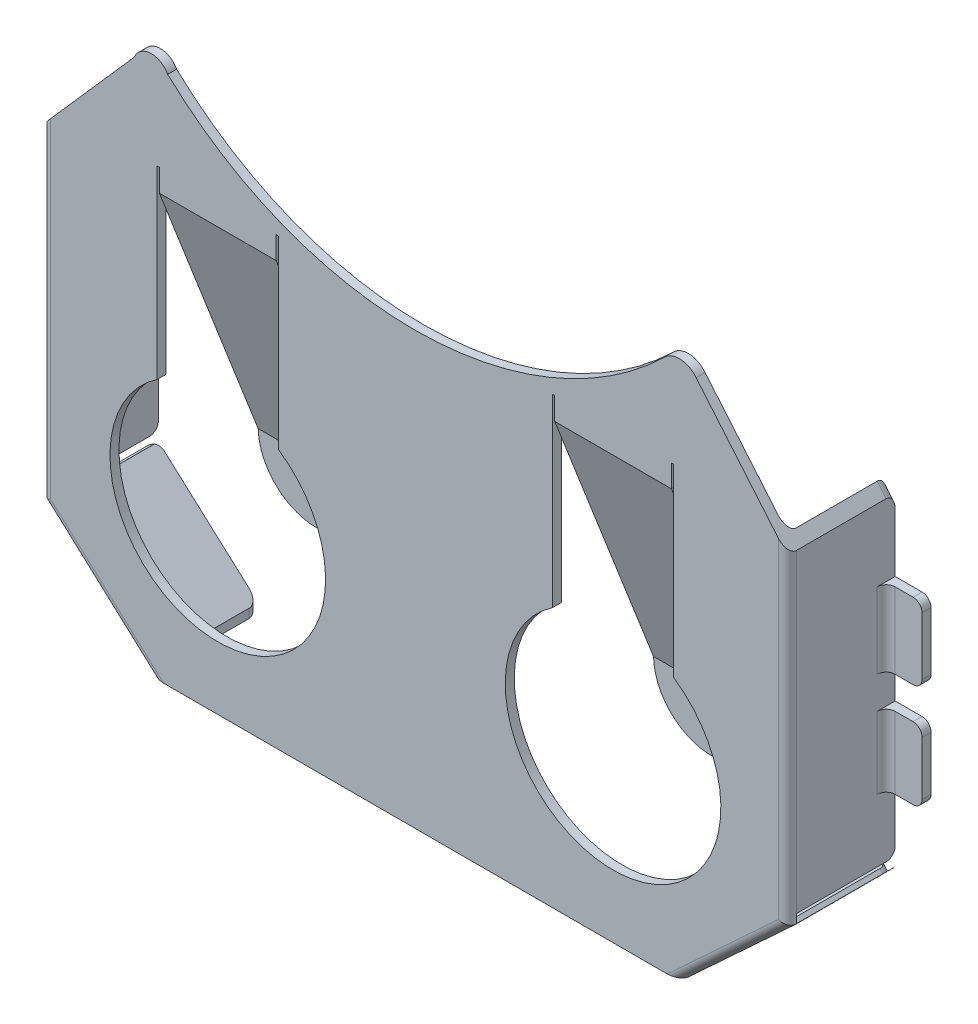
SolidWorks part; units mm, degrees
ref_plane "Front Plane" through (0, 0, 0) normal (0, 0, 1) x (1, 0, 0)
ref_plane "Top Plane" through (0, 0, 0) normal (0, 1, 0) x (1, 0, 0)
ref_plane "Right Plane" through (0, 0, 0) normal (1, 0, 0) x (0, 0, -1)
sketch "Sketch1" plane through (0, 0, 0) normal (0, 0, 1) x (1, 0, 0)
  line L0 (-0.8513, 0) -> (14.1347, 0)
  line L2 (-3.9254, 2.794) -> (-3.9254, 11.938)
  line L3 (-3.9254, 12.065) -> (17.1566, 12.065) construction
  line L4 (17.1566, 2.794) -> (17.1566, 11.938)
  line L5 (14.1347, 0) -> (14.1347, 15.2374)
  line L6 (-0.8513, 0) -> (-0.8513, 15.2392)
  line L7 (-3.9254, 11.938) -> (-1.3073, 14.913)
  line L8 (-0.8513, 0) -> (-3.9254, 2.794)
  line L9 (17.1566, 11.938) -> (14.5779, 15.0065)
  line L10 (14.1347, 0) -> (17.1566, 2.794)
  arc A2 (-0.3623, 14.9648) -> (13.6714, 15.0504) centre (6.6097, 22.3651) ccw
  arc A3 (-1.3073, 14.913) -> (-0.3623, 14.9648) centre (-0.8226, 14.7174) cw
  arc A5 (14.5779, 15.0065) -> (13.6714, 15.0504) centre (14.1059, 14.6414) ccw
  point P0 (-0.8513, 15.2392)
  dimension "D1" = 21.082
  dimension "D2" = 14.986
extrude "Boss-Extrude1" add sketch "Sketch1" along normal blind 3.048 separate body contours L3 L7 L2 L8 L6 | L3 L6 L0 L5 | L3 L5 L10 L4 L9 | L7 L3 L6 A3 | L6 L3 L5 A5 A2 A3 | L5 L3 L9 A5
sketch "Sketch2" plane through (0, 0, 0) normal (0, 0, 1) x (1, 0, 0)
  circle A2 centre (12.2297, 4.826) radius 3.048
  circle A3 centre (1.0537, 4.826) radius 3.048
extrude "Cut-Extrude1" cut sketch "Sketch2" against normal through all and the other way through all contours A3 | A2
sketch "Sketch3" plane through (0, 0, 0) normal (0, 0, 1) x (1, 0, 0)
  line L0 (-3.6714, 11.938) -> (-3.6714, 17.4811)
  line L1 (-3.6714, 11.938) -> (-3.6714, 2.794)
  line L3 (-0.8513, 0.254) -> (-3.6714, 2.794)
  line L7 (14.1347, 0.254) -> (-0.8513, 0.254)
  line L9 (16.9026, 2.794) -> (14.1347, 0.254)
  line L10 (16.9026, 11.938) -> (16.9026, 17.4811)
  line L11 (16.9026, 11.938) -> (16.9026, 2.794)
  line L12 (-3.6714, 17.4811) -> (16.9026, 17.4811)
  point P4 (0, 0)
sketch "Sketch4" plane through (0, 0, 0) normal (0, 0, 1) x (1, 0, 0)
  line L1 (17.1566, 2.794) -> (17.1566, 11.938) construction
  line L2 (17.1566, 4.826) -> (18.1726, 4.826)
  line L3 (18.1726, 4.826) -> (18.1726, 6.858)
  line L4 (18.1726, 6.858) -> (17.1566, 6.858)
  line L5 (17.1566, 6.858) -> (17.1566, 4.826)
  line L6 (18.1726, 9.906) -> (18.1726, 7.7657)
  line L7 (18.1726, 7.7657) -> (17.1566, 7.7657)
  line L8 (17.1566, 7.7657) -> (17.1566, 9.906)
  line L9 (17.1566, 9.906) -> (18.1726, 9.906)
extrude "Boss-Extrude2" add sketch "Sketch4" along normal blind 0.254
fillet "Fillet1" radius 0.254 2 edges at (17.1566, 5.842, 0.254) (17.1566, 8.8359, 0.254)
fillet "Fillet2" radius 0.254 4 edges at (18.1726, 6.858, 0.127) (18.1726, 4.826, 0.127) (18.1726, 7.7657, 0.127) (18.1726, 9.906, 0.127)
extrude "Cut-Extrude3" cut sketch "Sketch3" along normal blind 2.794
ref_plane "Plane1" through (6.731, 0, 0) normal (1, 0, 0) x (0, 0, -1)
mirror "Mirror3" about plane through (6.731, 0, 0) normal (1, 0, 0) of "Boss-Extrude2"
fillet "Fillet4" radius 0.254 2 edges at (-3.9254, 5.842, 0.254) (-3.9254, 8.8359, 0.254)
fillet "Fillet5" radius 0.254 4 edges at (-4.7106, 4.826, 0.127) (-4.7106, 6.858, 0.127) (-4.7106, 7.7657, 0.127) (-4.7106, 9.906, 0.127)
sketch "Sketch5" plane through (0, 0, 0) normal (0, -1, 0) x (-1, 0, 0)
  line L2 (0.8513, -3.048) -> (0.8513, 0) construction
  line L4 (0.8513, -2.794) -> (-14.1347, -2.794)
  line L5 (0.8513, -2.794) -> (0.8513, 0)
  line L6 (0.8513, 0) -> (-14.1347, 0)
  line L7 (-14.1347, -2.794) -> (-14.1347, 0)
  point P11 (0, 0)
extrude "Cut-Extrude4" cut sketch "Sketch5" against normal blind 0.254
fillet "Fillet6" radius 0.254 4 edges at (14.1347, 0.127, 2.794) (14.1347, 0.127, 0) (-0.8513, 0.127, 0) (-0.8513, 0.127, 2.794)
fillet "Fillet7" radius 0.254 8 edges at (-2.3883, 1.397, 3.048) (15.6457, 1.397, 3.048) (17.1566, 7.366, 3.048) (-3.9254, 7.366, 3.048) (-3.6714, 7.5103, 2.794) (16.9026, 7.5171, 2.794) (17.0296, 12.0891, 0) (-3.7984, 12.0823, 0)
sketch "Sketch9" plane through (17.1566, 0, 0) normal (1, 0, 0) x (0, 0, -1)
  line L2 (-2.794, 2.7965) -> (-2.794, 3.0473)
  line L3 (0, 2.794) -> (0, 4.826) construction
  line L4 (-2.794, 2.7965) -> (0, 2.7965)
  line L5 (-2.794, 11.938) -> (-2.794, 2.794) construction
  line L7 (0, 3.0473) -> (0, 2.7965)
  line L11 (-2.794, 3.0473) -> (0, 3.0473)
extrude "Cut-Extrude16" cut sketch "Sketch9" against normal through all
ref_plane "Plane2" through (-0.3851, -0.4237, 0) normal (-0.6726, -0.74, 0) x (-0.74, 0.6726, 0)
sketch "Sketch11" plane through (-0.3851, -0.4237, 0) normal (-0.6726, -0.74, 0) x (-0.74, 0.6726, 0)
  line L0 (4.7841, -2.794) -> (4.6373, -2.794)
  line L1 (0.63, -2.794) -> (4.7841, -2.794) construction
  line L2 (4.6373, -2.794) -> (4.6373, 0)
  line L3 (0.9732, 0) -> (4.7841, 0) construction
  line L4 (4.6373, 0) -> (4.7841, 0)
  line L5 (4.7841, 0) -> (4.7841, -2.794)
  line L6 (4.6373, -2.794) -> (4.7841, -2.794)
  line L7 (4.6373, -2.794) -> (4.5103, -2.794)
  line L8 (4.5103, -2.794) -> (4.5103, 0)
  line L9 (4.5103, 0) -> (4.6373, 0)
extrude "Cut-Extrude17" cut sketch "Sketch11" against normal blind 0.1524 contours L5 L4 L2 L0
ref_plane "Plane3" through (6.5144, -7.0457, 0) normal (0.6789, -0.7342, 0) x (-0.7342, -0.6789, 0)
sketch "Sketch12" plane through (6.5144, -7.0457, 0) normal (0.6789, -0.7342, 0) x (-0.7342, -0.6789, 0)
  line L0 (-14.494, -2.794) -> (-14.367, -2.794)
  line L1 (-14.494, -2.794) -> (-10.3784, -2.794) construction
  line L2 (-14.367, -2.794) -> (-14.367, 0)
  line L3 (-10.7243, 0) -> (-14.494, 0) construction
  line L4 (-14.367, 0) -> (-14.494, 0)
  line L5 (-14.494, 0) -> (-14.494, -2.794)
extrude "Cut-Extrude18" cut sketch "Sketch12" against normal blind 0.127
fillet "Fillet8" radius 0.254 6 edges at (16.9026, 2.7953, 0) (-3.6714, 2.7953, 0) (16.9419, 2.7965, 0) (-3.6981, 2.7965, 0) (-3.7707, 2.7459, 0) (17.0223, 2.7522, 0)
fillet "Fillet9" radius 0.254 2 edges at (-3.7984, 3.0473, 0) (17.0296, 3.0473, 0)
sketch "Sketch13" plane through (0, 0, 0) normal (0, 0, 1) x (1, 0, 0)
  line L0 (-0.5973, 11.938) -> (2.7047, 11.938)
  line L1 (-0.5973, 4.826) -> (-0.6608, 4.826)
  line L2 (10.5787, 4.826) -> (10.5152, 4.826)
  line L3 (-0.5973, 4.826) -> (2.7047, 4.826)
  line L4 (10.5152, 4.826) -> (10.5152, 11.938)
  line L6 (10.5787, 11.938) -> (13.8807, 11.938)
  line L8 (13.8807, 4.826) -> (10.5787, 4.826)
  line L9 (-0.6608, 4.826) -> (-0.6608, 11.938)
  line L10 (-0.6608, 11.938) -> (-0.5973, 11.938)
  line L11 (2.7047, 4.826) -> (2.7682, 4.826)
  line L12 (2.7682, 4.826) -> (2.7682, 11.938)
  line L13 (2.7682, 11.938) -> (2.7047, 11.938)
  line L14 (10.5152, 11.938) -> (10.5787, 11.938)
  line L15 (13.8807, 4.826) -> (13.9442, 4.826)
  line L16 (13.9442, 4.826) -> (13.9442, 11.938)
  line L17 (13.9442, 11.938) -> (13.8807, 11.938)
extrude "Cut-Extrude19" cut sketch "Sketch13" along normal through all
sketch "Sketch14" plane through (0, 0, 0) normal (0, 0, 1) x (1, 0, 0)
  line L0 (-0.6608, 11.938) -> (-0.5973, 11.938)
  line L1 (2.7682, 11.938) -> (-0.6608, 11.938) construction
  line L2 (-0.5973, 11.938) -> (-0.5973, 12.573)
  line L3 (2.7682, 11.938) -> (2.7047, 11.938)
  line L4 (2.7047, 11.938) -> (2.7047, 12.573)
  line L5 (2.7047, 12.573) -> (2.7682, 12.573)
  line L6 (2.7682, 12.573) -> (2.7682, 11.938)
  line L7 (-0.5973, 12.573) -> (-0.6608, 12.573)
  line L8 (-0.6608, 12.573) -> (-0.6608, 11.938)
  line L9 (10.5152, 11.938) -> (10.5787, 11.938)
  line L10 (13.9442, 11.938) -> (10.5152, 11.938) construction
  line L11 (10.5787, 11.938) -> (10.5787, 12.573)
  line L12 (10.5787, 12.573) -> (10.5152, 12.573)
  line L13 (10.5152, 12.573) -> (10.5152, 11.938)
  line L14 (13.9442, 11.938) -> (13.8807, 11.938)
  line L15 (13.8807, 11.938) -> (13.8807, 12.573)
  line L16 (13.8807, 12.573) -> (13.9442, 12.573)
  line L17 (13.9442, 12.573) -> (13.9442, 11.938)
extrude "Cut-Extrude20" cut sketch "Sketch14" along normal through all contours L12 L13 L9 L11 | L17 L16 L15 L14 | L7 L8 L0 L2 | L6 L5 L4 L3
sketch "Sketch15" plane through (0, 0, 0) normal (0, 0, 1) x (1, 0, 0)
  line L0 (-0.5973, 4.826) -> (2.7047, 4.826)
  line L1 (10.5787, 4.826) -> (13.8807, 4.826)
  arc A1 (-0.5973, 4.826) -> (2.7047, 4.826) centre (1.0537, 4.826) ccw
  arc A2 (10.5787, 4.826) -> (13.8807, 4.826) centre (12.2297, 4.826) ccw
extrude "Boss-Extrude3" add sketch "Sketch15" along normal blind 0.254 separate body
sketch "Sketch18" plane through (6.731, 0, 0) normal (1, 0, 0) x (0, 0, -1)
  line L0 (-2.9271, 11.9804) -> (-0.1166, 4.7831)
  point P2 (-2.9144, 11.9756)
  point P3 (0, 4.856)
  point P4 (-0.3933, 4.863)
  point P5 (-0.1259, 4.7803)
  point P6 (0, 4.6173)
  point P7 (-3.048, 11.8354)
  point P8 (-3.048, 11.7597)
  point P9 (-3.048, 11.7758)
  point P10 (0, 4.8838)
  point P11 (-0.1239, 4.7876)
  point P12 (-2.9272, 11.9857)
  point P13 (-2.9118, 11.9807)
  point P14 (-2.9353, 11.979)
  point P15 (-2.9271, 11.9804)
  point P16 (0, 0)
  point P17 (-0.114, 4.7809)
  point P18 (-0.1168, 4.7811)
  point P19 (-0.1106, 4.7756)
  point P20 (-0.1217, 4.7816)
  point P21 (-0.1166, 4.7831)
extrude "Extrude-Thin1" add sketch "Sketch18" along normal mid plane 3.302 from offset 5.4988 thin thin type mid plane wall 0.254
sketch "Sketch20" plane through (6.731, 0, 0) normal (1, 0, 0) x (0, 0, -1)
  line L0 (-2.8102, 12.0309) -> (0, 4.8252)
  point P2 (-2.7696, 12.0291)
  point P3 (-2.7605, 12.0333)
  point P4 (-3.048, 11.9387)
  point P5 (-2.8041, 12.0339)
  point P6 (0, 4.8252)
  point P7 (0, 0)
  point P8 (-2.8101, 12.0318)
  point P9 (-2.8102, 12.0309)
extrude "Extrude-Thin2" add sketch "Sketch20" along normal mid plane 3.302 from offset 5.6787 thin offset against normal yes
sketch "Bend-Lines1" plane through (0, 0, 0) normal (0, 1, 0) x (1, 0, 0)
sketch "Bounding-Box1" plane through (0, 0, 0) normal (0, 1, 0) x (1, 0, 0)
